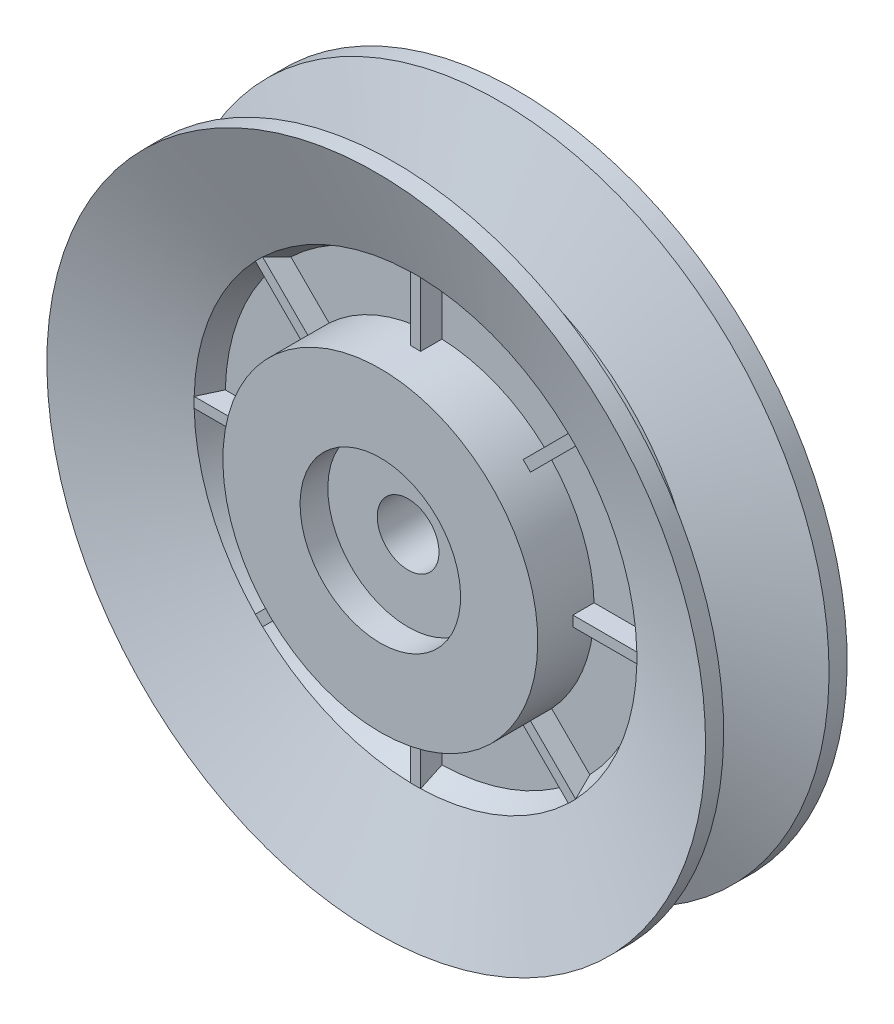
SolidWorks part; units mm, degrees
ref_plane "Front Plane" through (0, 0, 0) normal (0, 0, 1) x (1, 0, 0)
ref_plane "Top Plane" through (0, 0, 0) normal (0, 1, 0) x (1, 0, 0)
ref_plane "Right Plane" through (0, 0, 0) normal (1, 0, 0) x (0, 0, -1)
sketch "Sketch1" plane through (0, 0, 0) normal (1, 0, 0) x (0, 0, -1)
  line L0 (0, 0) -> (20.574, 0) construction
  line L1 (18.415, 50.8) -> (21.209, 50.8)
  line L2 (0, 12.3812) -> (4.287, 12.3812)
  line L3 (7.521, 36.068) -> (13.053, 36.068)
  line L4 (-0.635, 50.8) -> (2.159, 50.8)
  line L5 (20.574, 12.3813) -> (20.574, 24.287)
  line L6 (5.4258, 34.1481) -> (8.6995, 32.6215)
  line L7 (2.159, 50.8) -> (7.521, 36.068)
  line L8 (4.287, 12.3812) -> (4.287, 20)
  line L9 (18.415, 50.8) -> (13.053, 36.068)
  line L10 (11.8745, 32.6215) -> (15.1482, 34.1481)
  line L11 (0, 24.287) -> (8.6995, 24.287)
  line L12 (4.287, 20) -> (16.287, 20)
  line L13 (0, 12.3812) -> (0, 24.287)
  line L14 (8.6995, 24.287) -> (11.8745, 24.287) construction
  line L15 (16.287, 20) -> (16.287, 12.3813)
  line L16 (16.287, 4.7625) -> (4.287, 4.7625) construction
  line L17 (11.8745, 24.287) -> (20.574, 24.287)
  line L18 (11.8745, 32.6215) -> (11.8745, 24.287)
  line L19 (8.6995, 32.6215) -> (8.6995, 24.287)
  line L20 (5.4258, 34.1481) -> (-0.635, 50.8)
  line L21 (15.1482, 34.1481) -> (21.209, 50.8)
  line L22 (1.9526, 51.367) -> (18.6214, 51.367) construction
  line L23 (16.287, 12.3813) -> (20.574, 12.3813)
  line L24 (4.287, 4.7625) -> (4.287, 20) construction
  line L25 (16.287, 20) -> (16.287, 4.7625) construction
  line L26 (18.6214, 51.367) -> (14.8657, 41.0483) construction
  line L27 (7.521, 36.068) -> (5.0538, 35.17) construction
  line L28 (10.287, 36.068) -> (10.287, 0) construction
  line L29 (4.287, 20) -> (4.287, 24.287) construction
  line L30 (5.7083, 41.0483) -> (1.9526, 51.367) construction
  line L31 (10.287, 41.0483) -> (10.287, 51.367) construction
  line L32 (5.7083, 41.0483) -> (14.8657, 41.0483) construction
  line L33 (7.521, 36.068) -> (6.4114, 33.6885) construction
  point P10 (10.287, 20)
  point P12 (10.287, 24.287)
  dimension "D1" = 40
  dimension "A" = 101.6
  dimension "B" = 72.136
  dimension "C" = 16.256
  dimension "D" = 21.844
  dimension "D2" = 3.175
  dimension "D3" = 130
  dimension "D4" = 40
  dimension "D5" = 12
  dimension "Bore" = 9.525
  dimension "E" = 20.574
  dimension "Belt Width" = 16.6687
  dimension "Belt Heigth" = 10.3187
revolve "Revolve1" add sketch "Sketch1" angle 360 about L0
sketch "Sketch2" plane through (0, 0, 0) normal (1, 0, 0) x (0, 0, -1)
  line L0 (0, 0) -> (20.574, 0) construction
  line L2 (4.287, 20) -> (16.287, 20)
  line L3 (4.287, 20) -> (4.287, 4.7625)
  line L4 (4.287, 4.7625) -> (16.287, 4.7625)
  line L5 (16.287, 20) -> (16.287, 4.7625)
revolve "Revolve2" add sketch "Sketch2" angle 360 about L0
sketch "Sketch4" plane through (0, 0, 0) normal (1, 0, 0) x (0, 0, -1)
  line L0 (8.6995, 32.6215) -> (8.6995, 24.287) construction
  line L1 (0, 24.287) -> (8.6995, 24.287) construction
  line L2 (8.6995, 32.6215) -> (8.6995, 24.287)
  line L3 (5.4258, 24.287) -> (8.6995, 24.287) construction
  line L4 (5.4258, 34.1481) -> (8.6995, 32.6215) construction
  line L5 (10.287, 36.068) -> (10.287, 24.287) construction
  line L6 (8.6995, 24.287) -> (8.6995, 23.017)
  line L7 (8.6995, 23.017) -> (5.4258, 23.017)
  line L9 (5.4258, 23.017) -> (5.4258, 24.287)
  line L10 (15.1482, 23.017) -> (15.1482, 24.287)
  line L11 (11.8745, 23.017) -> (15.1482, 23.017)
  line L12 (11.8745, 24.287) -> (11.8745, 23.017)
  line L14 (11.8745, 32.6215) -> (11.8745, 24.287)
  line L16 (5.4258, 34.1481) -> (8.6995, 32.6215)
  line L17 (5.4258, 34.1481) -> (5.4258, 24.287)
  line L19 (7.521, 36.068) -> (13.053, 36.068) construction
  line L20 (15.1482, 34.1481) -> (15.1482, 24.287)
  line L21 (15.1482, 34.1481) -> (11.8745, 32.6215)
  dimension "D1" = 1.27
extrude "Boss-Extrude2" add sketch "Sketch4" along normal mid plane 1.5875
pattern_circular "CirPattern1" count 8 over 360 about axis through (0, 0, 0) along (0, 0, 1) of "Boss-Extrude2"
